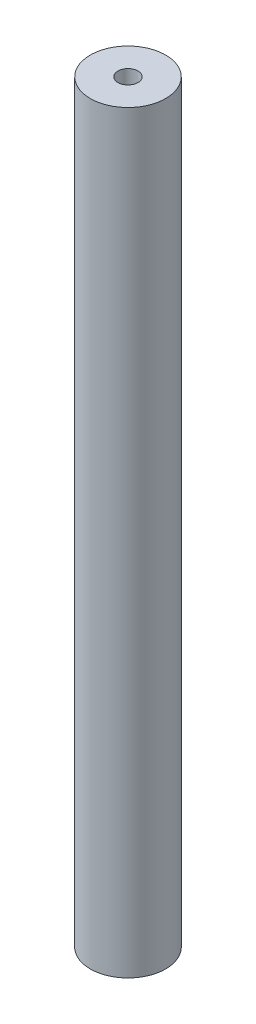
SolidWorks part; units mm, degrees
ref_plane "Alzado" through (0, 0, 0) normal (0, 0, 1) x (1, 0, 0)
ref_plane "Planta" through (0, 0, 0) normal (0, 1, 0) x (1, 0, 0)
ref_plane "Vista lateral" through (0, 0, 0) normal (1, 0, 0) x (0, 0, -1)
sketch "Croquis1" plane through (0, 0, 0) normal (0, 1, 0) x (1, 0, 0)
  circle A0 centre (0, 0) radius 15
  circle A1 centre (0, 0) radius 4
  dimension "D1" = 30
  dimension "D2" = 8
extrude "Saliente-Extruir1" add sketch "Croquis1" along normal blind 300
